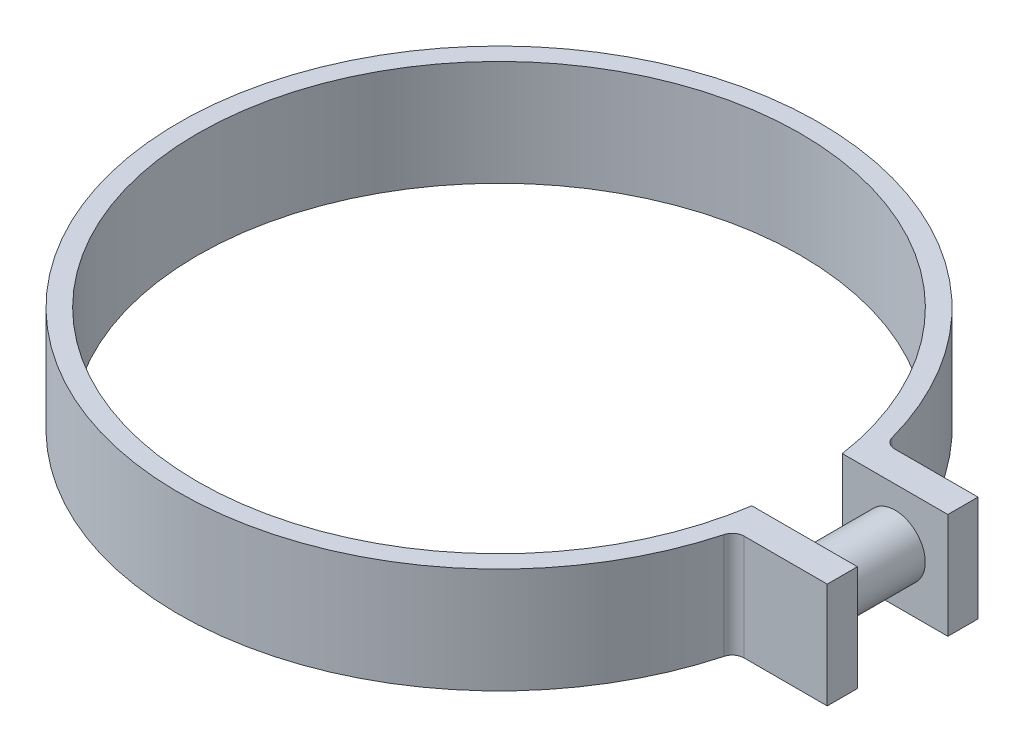
SolidWorks part; units mm, degrees
ref_plane "Front Plane" through (0, 0, 0) normal (0, 0, 1) x (1, 0, 0)
ref_plane "Top Plane" through (0, 0, 0) normal (0, 1, 0) x (1, 0, 0)
ref_plane "Right Plane" through (0, 0, 0) normal (1, 0, 0) x (0, 0, -1)
sketch "Sketch1" plane through (0, 0, 0) normal (0, 1, 0) x (1, 0, 0)
  line L0 (0, 0) -> (25.4, 0) construction
  line L1 (34.0026, 3.81) -> (25.1126, 3.81)
  line L2 (34.0026, 3.81) -> (34.0026, 6.35)
  line L3 (34.0026, 6.35) -> (43.5684, 6.35) construction
  line L4 (34.0026, 6.35) -> (26.9875, 6.35)
  line L5 (26.9875, 3.81) -> (26.9875, 7.5413) construction
  line L6 (34.0026, -3.81) -> (25.1126, -3.81)
  line L7 (34.0026, -3.81) -> (34.0026, -6.35)
  line L8 (34.0026, -6.35) -> (26.9875, -6.35)
  line L9 (26.9875, 0) -> (26.9875, 3.81) construction
  line L10 (25.4, 0) -> (26.9875, 0) construction
  line L11 (26.9875, 0) -> (38.6979, 0) construction
  arc A0 (25.1126, 3.81) -> (25.1126, -3.81) centre (0, 0) ccw
  arc A1 (26.0447, 7.071) -> (26.0447, -7.071) centre (0, 0) ccw
  arc A2 (26.9875, 6.35) -> (26.0447, 7.071) centre (26.9875, 7.3269) cw
  arc A3 (26.9875, -6.35) -> (26.0447, -7.071) centre (26.9875, -7.3269) ccw
  arc A4 (26.9875, 0) -> (26.7172, 3.81) centre (0, 0) ccw construction
  arc A5 (26.7172, -3.81) -> (26.9875, 0) centre (0, 0) ccw construction
  arc A6 (25.4, 0) -> (25.1126, 3.81) centre (0, 0) ccw construction
  arc A7 (25.1126, -3.81) -> (25.4, 0) centre (0, 0) ccw construction
  arc A8 (26.0447, -7.071) -> (26.7172, -3.81) centre (0, 0) ccw construction
  point P12 (0, 0)
  dimension "D1" = 50.8
  dimension "D2" = 1.5875
  dimension "D3" = 8.89
  dimension "D4" = 2.54
  dimension "D5" = 3.81
extrude "Boss-Extrude1" add sketch "Sketch1" along normal mid plane 8.89
sketch "Sketch2" plane through (0, 0, -3.81) normal (0, 0, 1) x (1, 0, 0)
  line L0 (25.1126, -4.445) -> (34.0026, -4.445) construction
  line L1 (25.1126, -4.445) -> (34.0026, -4.445) construction
  line L2 (25.1126, -4.445) -> (25.1126, 4.445) construction
  line L3 (25.1126, 4.445) -> (34.0026, 4.445) construction
  line L4 (34.0026, -4.445) -> (34.0026, 4.445) construction
  line L5 (25.1126, -4.445) -> (34.0026, 4.445) construction
  line L6 (25.1126, 4.445) -> (34.0026, -4.445) construction
  circle A0 centre (29.5576, 0) radius 2.54
  dimension "D1" = 5.08
extrude "Boss-Extrude2" add sketch "Sketch2" along normal up to next
